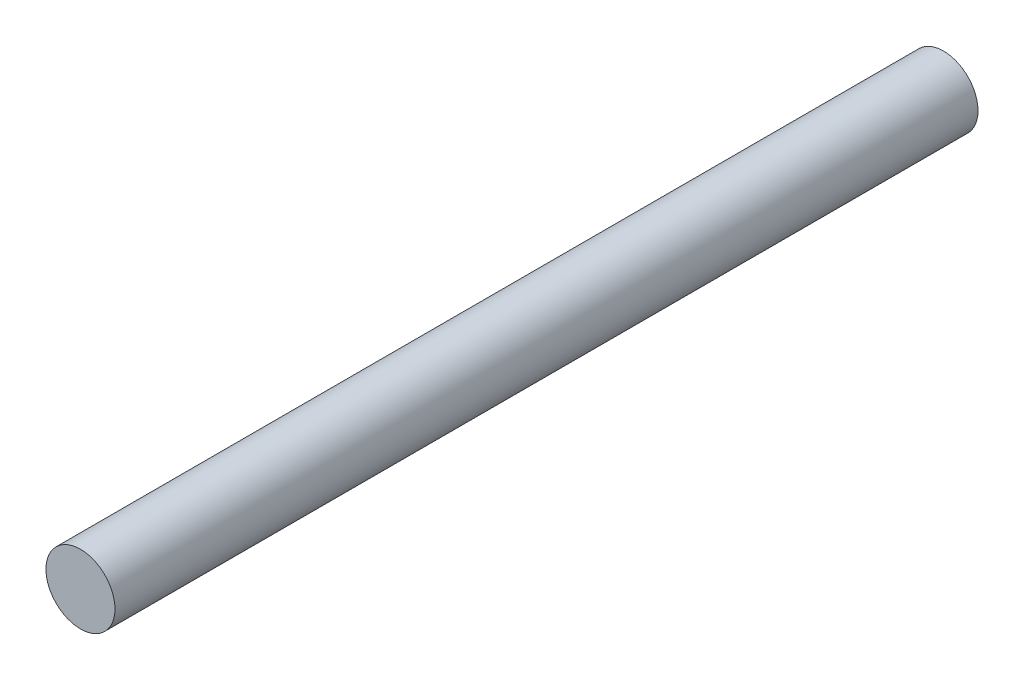
SolidWorks part; units mm, degrees
ref_plane "Plan de face" through (0, 0, 0) normal (0, 0, 1) x (1, 0, 0)
ref_plane "Plan de dessus" through (0, 0, 0) normal (0, 1, 0) x (1, 0, 0)
ref_plane "Plan de droite" through (0, 0, 0) normal (1, 0, 0) x (0, 0, -1)
sketch "Esquisse1" plane through (0, 0, 0) normal (0, 0, 1) x (1, 0, 0)
  circle A0 centre (33.9699, 0) radius 4
  dimension "D1" = 8
extrude "Boss.-Extru.1" add sketch "Esquisse1" along normal blind 100
